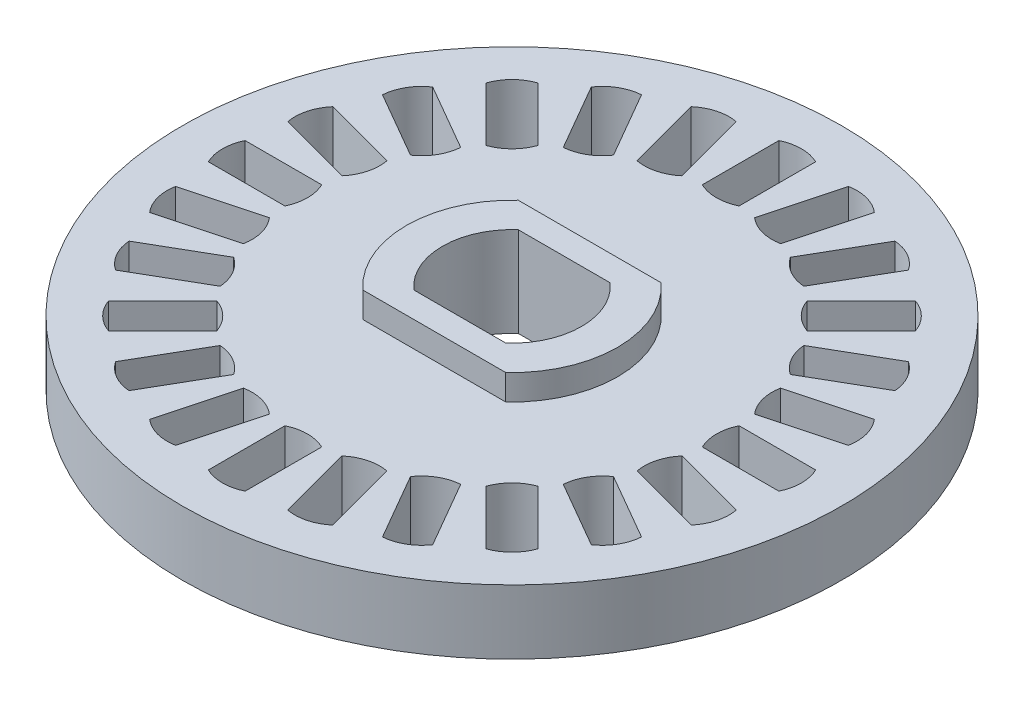
SolidWorks part; units mm, degrees
ref_plane "前视" through (0, 0, 0) normal (0, 0, 1) x (1, 0, 0)
ref_plane "上视" through (0, 0, 0) normal (0, 1, 0) x (1, 0, 0)
ref_plane "右视" through (0, 0, 0) normal (1, 0, 0) x (0, 0, -1)
sketch "草图1" plane through (0, 0, 0) normal (0, 1, 0) x (1, 0, 0)
  circle A0 centre (0, 0) radius 12.91
extrude "凸台-拉伸1" add sketch "草图1" along normal blind 2.52
sketch "草图2" plane through (0, 2.52, 0) normal (0, 1, 0) x (1, 0, 0)
  line L1 (-2.8, 3.045) -> (2.8, 3.045)
  line L3 (-2.8, -3.045) -> (2.8, -3.045)
  arc A0 (-2.8, -3.045) -> (-2.8, 3.045) centre (0, 0) cw
  arc A1 (2.8, -3.045) -> (2.8, 3.045) centre (0, 0) ccw
  point P0 (0, 0)
extrude "凸台-拉伸2" add sketch "草图2" along normal blind 1
sketch "草图3" plane through (0, 3.52, 0) normal (0, 1, 0) x (1, 0, 0)
  line L0 (-1.8, -2.045) -> (1.8, -2.045)
  line L1 (-1.8, 2.045) -> (1.8, 2.045)
  arc A0 (-1.8, -2.045) -> (-1.8, 2.045) centre (0, 0) cw
  arc A1 (1.8, -2.045) -> (1.8, 2.045) centre (0, 0) ccw
  point P0 (0, 0)
extrude "切除-拉伸1" cut sketch "草图3" against normal blind 4
sketch "草图4" plane through (0, 2.52, 0) normal (0, 1, 0) x (1, 0, 0)
  line L2 (-11.1752, -0.72) -> (-8.1752, -0.72)
  line L4 (-11.1752, 0.72) -> (-8.1752, 0.72)
  arc A2 (-11.1752, -0.72) -> (-11.1752, 0.72) centre (-9.6752, 0) cw
  arc A3 (-8.1752, -0.72) -> (-8.1752, 0.72) centre (-9.6752, 0) ccw
  point P5 (-9.6752, 0)
extrude "切除-拉伸2" cut sketch "草图4" against normal blind 4
pattern_circular "阵列(圆周)1" count 25 every 15 about axis through (0, 0, 0) along (0, 1, 0) of "切除-拉伸2"
